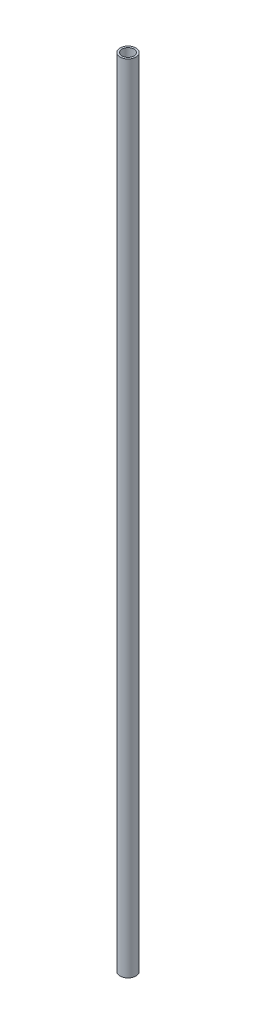
SolidWorks part; units mm, degrees
ref_plane "Front Plane" through (0, 0, 0) normal (0, 0, 1) x (1, 0, 0)
ref_plane "Top Plane" through (0, 0, 0) normal (0, 1, 0) x (1, 0, 0)
ref_plane "Right Plane" through (0, 0, 0) normal (1, 0, 0) x (0, 0, -1)
sketch "Sketch1" plane through (0, 0, 0) normal (0, 1, 0) x (1, 0, 0)
  circle A0 centre (0, 0) radius 2
  circle A1 centre (0, 0) radius 1.5
  dimension "D1" = 4
  dimension "D2" = 3
extrude "Boss-Extrude1" add sketch "Sketch1" along normal blind 200
